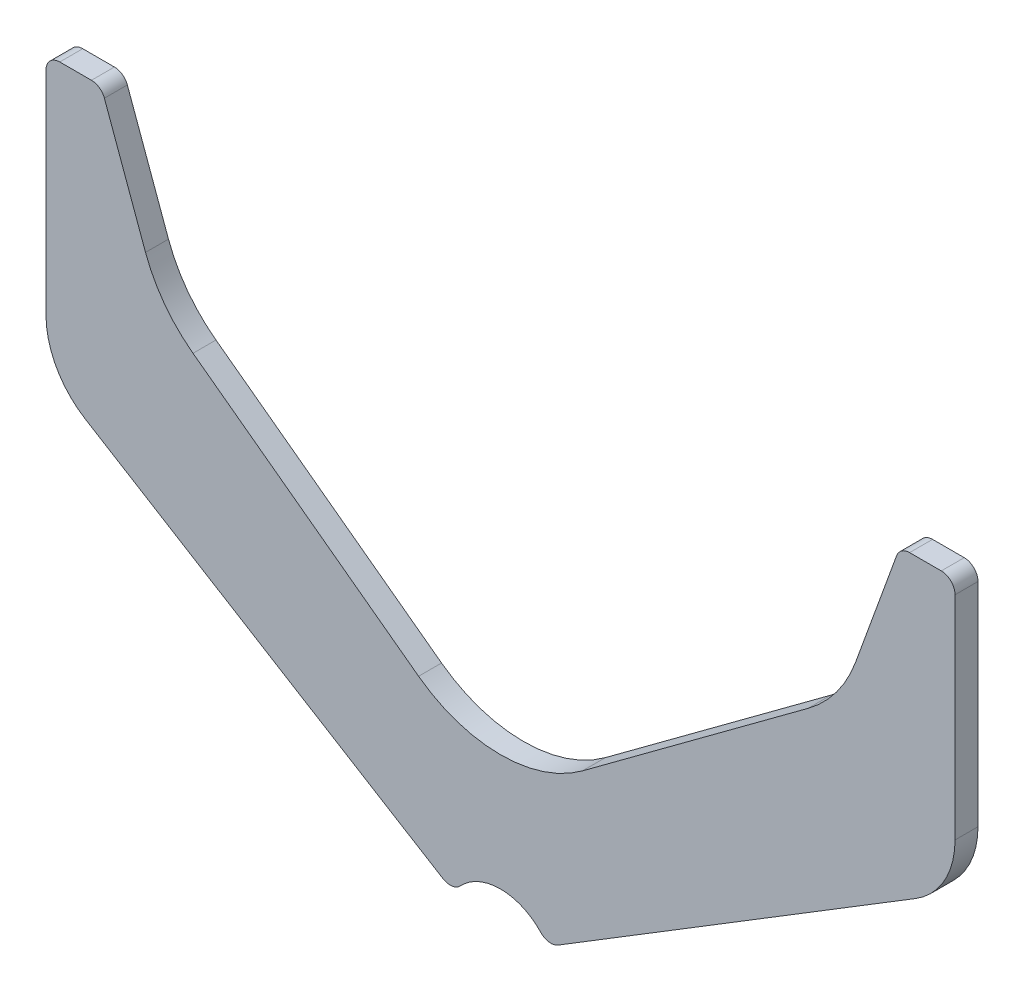
SolidWorks part; units mm, degrees
ref_plane "Plane1" through (0, 0, 0) normal (0, 0, 1) x (1, 0, 0)
ref_plane "Plane2" through (0, 0, 0) normal (0, 1, 0) x (1, 0, 0)
ref_plane "Plane3" through (0, 0, 0) normal (1, 0, 0) x (0, 0, -1)
sketch "Sketch1" plane through (0, 0, 0) normal (0, 0, 1) x (1, 0, 0)
  line L2 (-99, 117) -> (-99, 70.7478)
  line L3 (-90.405, 55.4002) -> (-12.5312, 7.6791)
  line L4 (0, 200) -> (0, 0) construction
  line L8 (-17.8447, 43.2044) -> (-66.9783, 79.5613)
  line L10 (-77.3244, 93.4164) -> (-86.2815, 118.0261)
  line L11 (-89.1006, 120) -> (-96, 120)
  line L13 (89.1006, 120) -> (96, 120)
  line L14 (77.3244, 93.4164) -> (86.2815, 118.0261)
  line L15 (17.8447, 43.2044) -> (66.9783, 79.5613)
  line L16 (90.405, 55.4002) -> (12.5312, 7.6791)
  line L17 (99, 117) -> (99, 70.7478)
  arc A0 (8.771, 8.1896) -> (-8.771, 8.1896) centre (0, 0) ccw
  arc A1 (12.5312, 7.6791) -> (8.771, 8.1896) centre (10.9637, 10.237) cw
  arc A2 (-12.5312, 7.6791) -> (-8.771, 8.1896) centre (-10.9637, 10.237) ccw
  arc A6 (-89.1006, 120) -> (-86.2815, 118.0261) centre (-89.1006, 117) cw
  arc A7 (-99, 117) -> (-96, 120) centre (-96, 117) cw
  arc A8 (86.2815, 118.0261) -> (89.1006, 120) centre (89.1006, 117) cw
  arc A9 (99, 117) -> (96, 120) centre (96, 117) ccw
  arc A10 (-90.405, 55.4002) -> (-99, 70.7478) centre (-81, 70.7478) cw
  arc A11 (99, 70.7478) -> (90.405, 55.4002) centre (81, 70.7478) cw
  arc A13 (66.9783, 79.5613) -> (77.3244, 93.4164) centre (49.1336, 103.677) ccw
  arc A14 (-77.3244, 93.4164) -> (-66.9783, 79.5613) centre (-49.1336, 103.677) ccw
  arc A15 (17.8447, 43.2044) -> (-17.8447, 43.2044) centre (0, 67.3201) cw
  point P3 (-87, 120)
  point P16 (-99, 120)
  point P34 (87, 120)
  point P37 (99, 120)
  point P40 (-99, 60.6673)
  point P43 (99, 60.6673)
  point P49 (74.2363, 84.932)
  point P52 (-74.2363, 84.932)
  point P55 (0, 30)
  dimension "D12" = 3
  dimension "D13" = 18
  dimension "D14" = 30
  dimension "D6" = 12
  dimension "D7" = 3
  dimension "D1" = 30
  dimension "D2" = 5
  dimension "D3" = 20
  dimension "D4" = 12
  dimension "D5" = 120
  dimension "D10" = 198
  dimension "D11" = 63
extrude "Base-Extrude" add sketch "Sketch1" along normal blind 5
